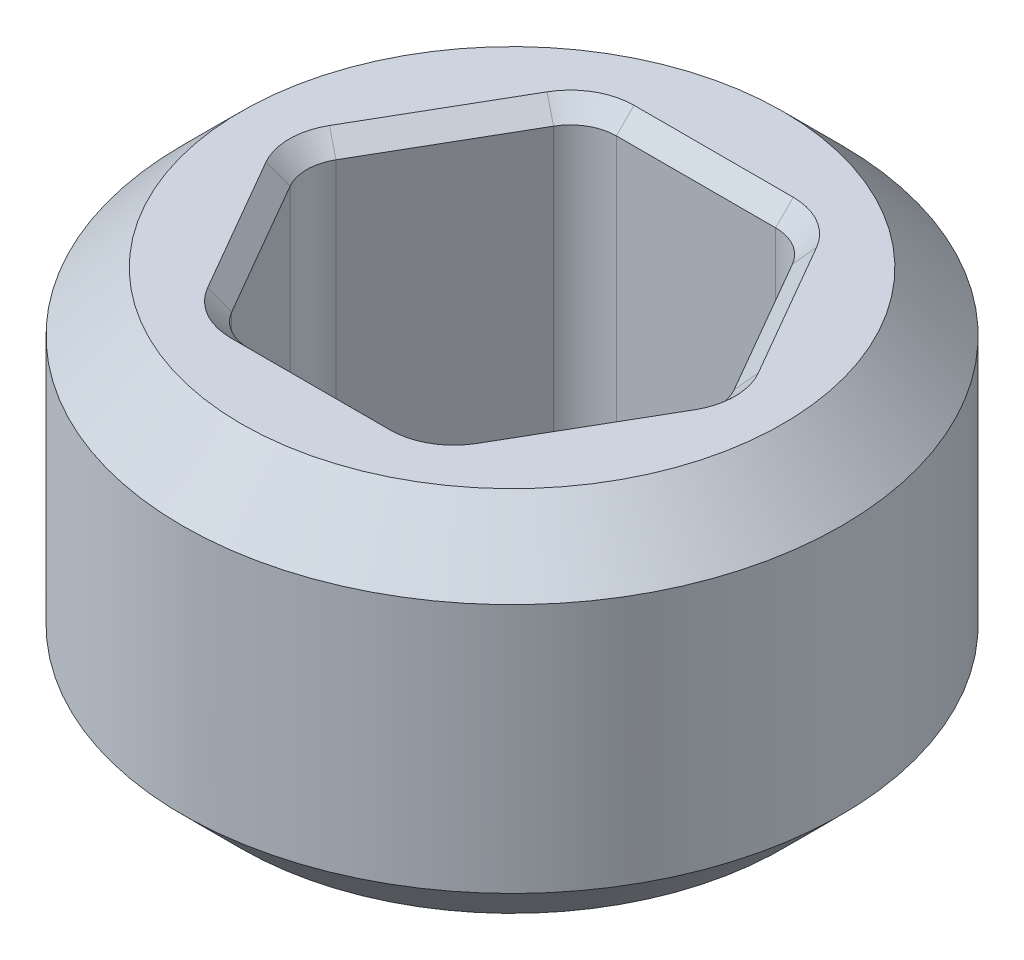
SolidWorks part; units mm, degrees
ref_plane "Front Plane" through (0, 0, 0) normal (0, 0, 1) x (1, 0, 0)
ref_plane "Top Plane" through (0, 0, 0) normal (0, 1, 0) x (1, 0, 0)
ref_plane "Right Plane" through (0, 0, 0) normal (1, 0, 0) x (0, 0, -1)
sketch "Sketch1" plane through (0, 0, 0) normal (0, 0, 1) x (1, 0, 0)
  line L0 (0, -1.7042) -> (0, -1.1626) construction
  line L1 (1.4224, -0.7938) -> (1.4224, 0.7938)
  line L2 (1.4224, 0.7938) -> (0, 0.7937)
  line L3 (0, 0.7937) -> (0, -0.7937)
  line L4 (0, -0.7937) -> (1.4224, -0.7938)
  dimension "D1" = 1.5875
  dimension "D2" = 2.8448
revolve "Revolve1" add sketch "Sketch1" angle 360 about L0
sketch "Sketch3" plane through (0, 0, 0) normal (0, 1, 0) x (1, 0, 0)
  line L1 (0.9165, 0) -> (0.4583, 0.7938)
  line L2 (0.4583, 0.7938) -> (-0.4583, 0.7937)
  line L3 (-0.4583, 0.7937) -> (-0.9165, 0)
  line L4 (-0.9165, 0) -> (-0.4583, -0.7938)
  line L5 (-0.4583, -0.7938) -> (0.4583, -0.7937)
  line L6 (0.4583, -0.7937) -> (0.9165, 0)
  circle A0 centre (0, 0) radius 0.7937 construction
  dimension "D1" = 1.5875
extrude "Cut-Extrude1" cut sketch "Sketch3" against normal through all both and the other way through all contours L2 L3 L4 L5 L6 L1
fillet "Fillet1" radius 0.1984 6 edges at (0.4583, 0, -0.7938) (0.9165, 0, 0) (0.4583, 0, 0.7937) (-0.4583, 0, 0.7938) (-0.9165, 0, 0) (-0.4583, 0, -0.7937)
chamfer "Chamfer1" distance 0.254 angle 45 2 edges at (0, -0.7938, -1.4224) (0, 0.7937, -1.4224)
chamfer "Chamfer2" distance 0.0762 angle 45 24 edges at (0.6874, 0.7937, -0.3969) (0.4429, 0.7937, -0.7672) (0.8858, 0.7937, 0) (0, 0.7937, -0.7937) (0.6874, 0.7937, 0.3969) (-0.4429, 0.7937, -0.7672) (0.4429, 0.7937, 0.7672) (-0.6874, 0.7937, -0.3969) (0, 0.7937, 0.7937) (-0.8858, 0.7937, 0) (-0.4429, 0.7937, 0.7672) (-0.6874, 0.7937, 0.3969) (0.6874, -0.7938, 0.3969) (0.8858, -0.7938, 0) (0.4429, -0.7938, 0.7672) (0.6874, -0.7938, -0.3969) (0, -0.7938, 0.7937) (0.4429, -0.7938, -0.7672) (-0.4429, -0.7938, 0.7672) (0, -0.7938, -0.7937) (-0.6874, -0.7938, 0.3969) (-0.4429, -0.7938, -0.7672) (-0.8858, -0.7938, 0) (-0.6874, -0.7938, -0.3969)
